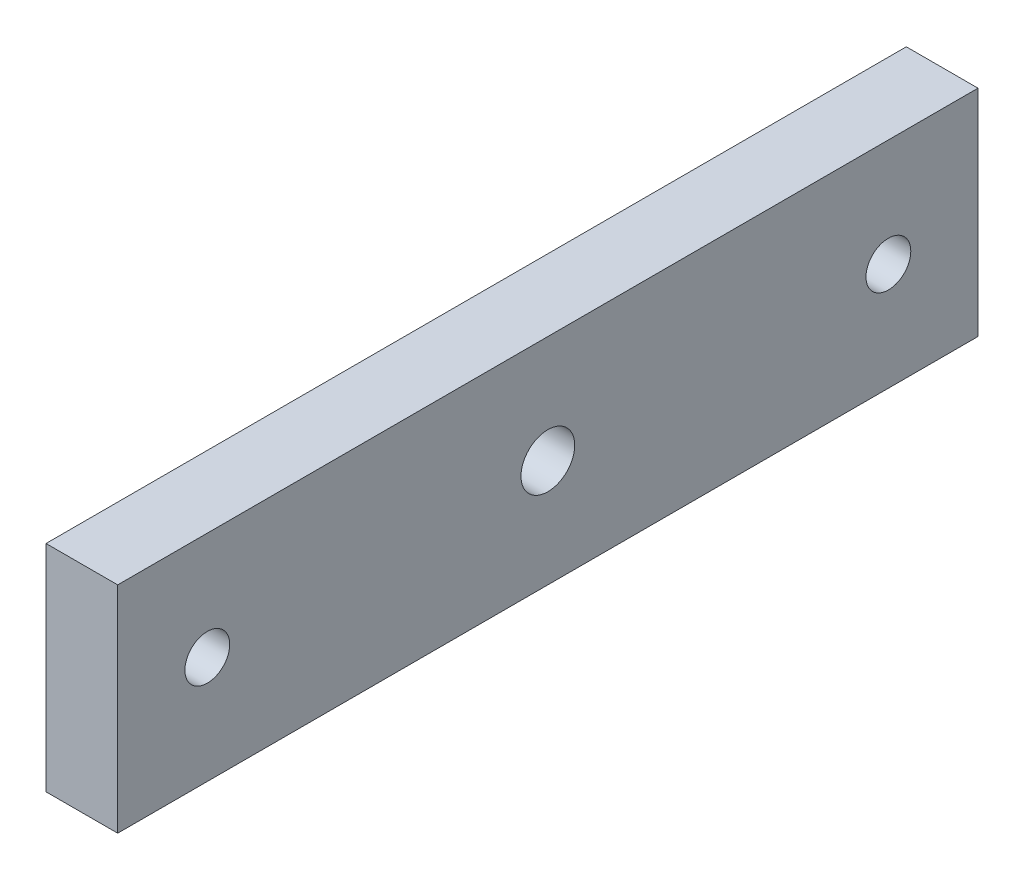
SolidWorks part; units mm, degrees
material "SS 304 (Default)"
ref_plane "Front Plane" through (0, 0, 0) normal (0, 0, 1) x (1, 0, 0)
ref_plane "Top Plane" through (0, 0, 0) normal (0, 1, 0) x (1, 0, 0)
ref_plane "Right Plane" through (0, 0, 0) normal (1, 0, 0) x (0, 0, -1)
sketch "Sketch1" plane through (0, 0, 0) normal (0, 0, 1) x (1, 0, 0)
  line L1 (-6.35, 19.05) -> (6.35, 19.05)
  line L2 (-6.35, 19.05) -> (-6.35, -19.05)
  line L3 (-6.35, -19.05) -> (6.35, -19.05)
  line L4 (6.35, 19.05) -> (6.35, -19.05)
  line L5 (-6.35, 19.05) -> (6.35, -19.05) construction
  line L6 (-6.35, -19.05) -> (6.35, 19.05) construction
  point P0 (0, 0)
  dimension "Width" = 12.7
  dimension "Height" = 38.1
extrude "Extrude1" add sketch "Sketch1" along normal mid plane 152.4
hole_wizard "3/8-16 Tapped Hole1" positions "Sketch3" profile "Sketch2" tap size "3/8-16" standard "ANSI Inch" end condition up to next
sketch "Sketch3" plane through (6.35, 0, 0) normal (1, 0, 0) x (0, 0, -1)
  line L0 (-60.325, 0) -> (60.325, 0) construction
  point P0 (-60.325, 0)
  point P1 (60.325, 0)
  point P7 (0, 0)
  dimension "D1" = 120.65
sketch "Sketch2" plane through (6.35, 0, 60.325) normal (0, 1, 0) x (0, 0, -1)
  line L0 (0, 0) -> (0, 12.7)
  line L1 (0, 12.7) -> (3.9687, 12.7)
  line L2 (3.9687, 12.7) -> (3.9687, 0)
  line L5 (3.9687, 0) -> (0, 0)
  line L11 (0, -6.35) -> (0, 107.95) construction
  dimension "Thru Tap Drill Dia." = 7.9375
  dimension "Thru Tap Drill Depth" = 12.7
cosmetic thread "Hole Thread1" parameters "D2"=9.525
cosmetic thread "Hole Thread2" parameters "D2"=9.525
hole_wizard "3/8 (0.375) Diameter Hole1" positions "Sketch5" profile "Sketch4" hole size "3/8" standard "Ansi Inch" end condition up to next
sketch "Sketch5" plane through (6.35, 0, 0) normal (1, 0, 0) x (0, 0, -1)
  point P0 (0, 0)
sketch "Sketch4" plane through (6.35, 0, 0) normal (0, 1, 0) x (0, 0, -1)
  line L0 (0, 0) -> (0, 12.7)
  line L1 (0, 12.7) -> (4.7625, 12.7)
  line L2 (4.7625, 12.7) -> (4.7625, 0)
  line L5 (4.7625, 0) -> (0, 0)
  line L11 (0, -6.35) -> (0, 107.95) construction
  dimension "Thru Hole Dia." = 9.525
  dimension "Thru Hole Depth" = 12.7
sketch "Sketch6" plane through (-6.35, 0, 0) normal (-1, 0, 0) x (0, 0, 1)
  circle A0 centre (0, 0) radius 12.827
  dimension "D1" = 25.654
extrude "Extrude2" cut sketch "Sketch6" against normal blind 3.175
